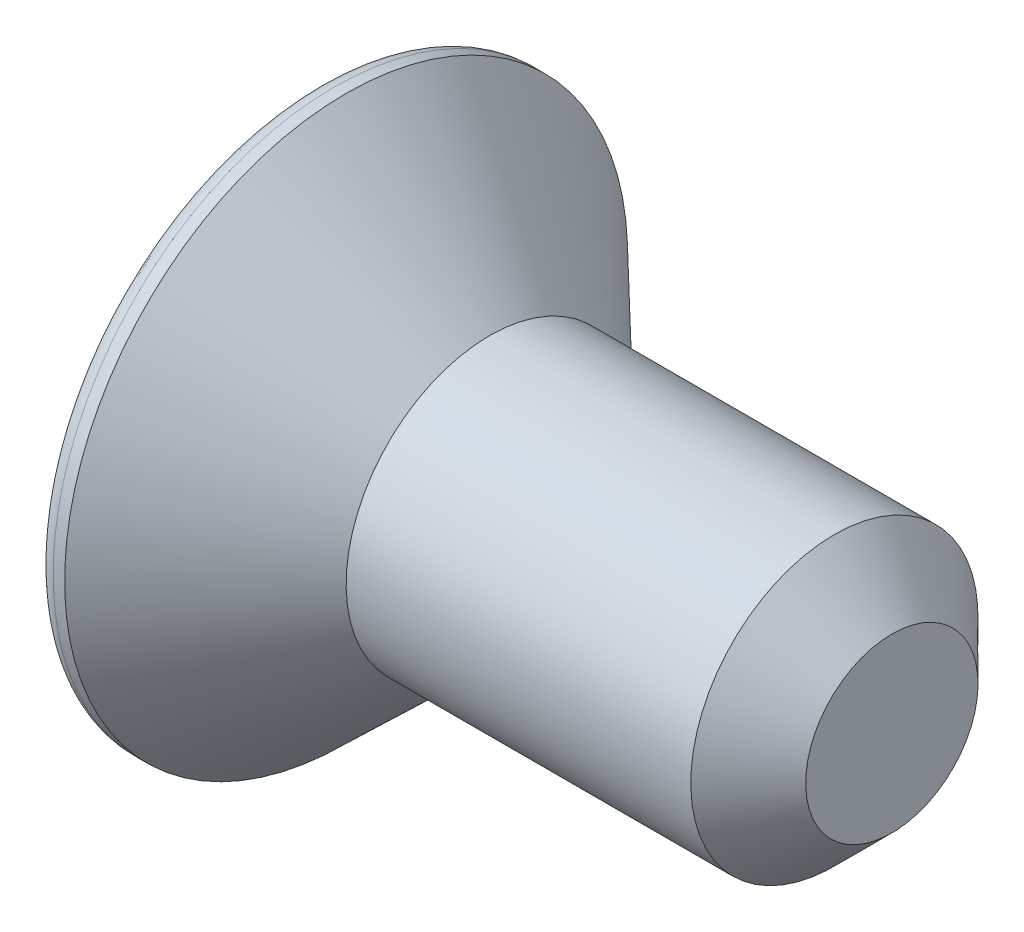
SolidWorks part; units mm, degrees
ref_plane "Спереди" through (0, 0, 0) normal (0, 0, 1) x (1, 0, 0)
ref_plane "Сверху" through (0, 0, 0) normal (0, 1, 0) x (1, 0, 0)
ref_plane "Справа" through (0, 0, 0) normal (1, 0, 0) x (0, 0, -1)
sketch "Эскиз1" plane through (0, 0, 0) normal (0, 0, 1) x (1, 0, 0)
  line L0 (0, 0) -> (0, 4.9)
  line L1 (0.5, 4.9) -> (3, 2.5)
  line L3 (3, 2.5) -> (10, 2.5)
  line L4 (10, 2.5) -> (10, 0)
  line L5 (10, 0) -> (0, 0)
  line L6 (0, 0) -> (10, 0) construction
  line L8 (0, 4.9) -> (0.5, 4.9)
  dimension "D4" = 0.5
  dimension "D1" = 3
  dimension "D2" = 2.5
  dimension "D3" = 4.9
  dimension "D5" = 10
revolve "Повернуть1" add sketch "Эскиз1" angle 360 about L5
cosmetic thread "Условное изображение резьбы1" parameters "D2"=4.11
sketch "Эскиз2" plane through (0, 0, 0) normal (-1, 0, 0) x (0, 0, 1)
  line L1 (0.866, 1.5) -> (-0.866, 1.5)
  line L2 (-0.866, 1.5) -> (-1.7321, 0)
  line L3 (-1.7321, 0) -> (-0.866, -1.5)
  line L4 (-0.866, -1.5) -> (0.866, -1.5)
  line L5 (0.866, -1.5) -> (1.7321, 0)
  line L6 (1.7321, 0) -> (0.866, 1.5)
  circle A0 centre (0, 0) radius 1.5 construction
  dimension "D1" = 3
extrude "Вырез-Вытянуть1" cut sketch "Эскиз2" against normal blind 2
fillet "Скругление1" radius 0.3 1 edges at (0, 4.9, 0)
chamfer "Фаска1" distance 1 angle 45 1 edges at (10, 2.5, 0)
